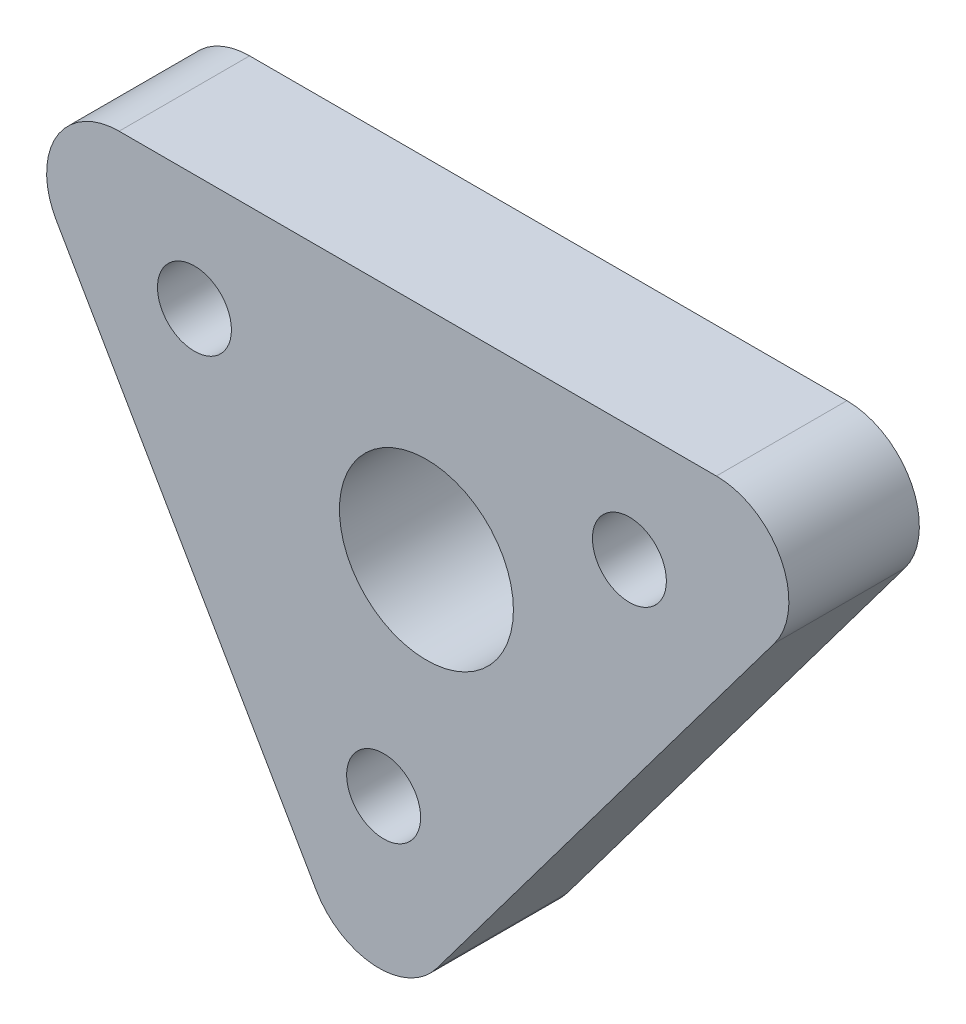
SolidWorks part; units mm, degrees
ref_plane "前视基准面" through (0, 0, 0) normal (0, 0, 1) x (1, 0, 0)
ref_plane "上视基准面" through (0, 0, 0) normal (0, 1, 0) x (1, 0, 0)
ref_plane "右视基准面" through (0, 0, 0) normal (1, 0, 0) x (0, 0, -1)
sketch "草图1" plane through (0, 0, 0) normal (0, 0, 1) x (1, 0, 0)
  line L0 (-40.197, 19.3205) -> (-10.197, 19.3205) construction
  line L1 (-54.0535, 27.3205) -> (5.803, 27.3205)
  line L2 (-27.1481, -3.2809) -> (-40.197, 19.3205) construction
  line L3 (-40.197, 19.3205) -> (-40.197, -20.6795) construction
  line L4 (-40.197, -20.6795) -> (-10.197, 19.3205) construction
  line L5 (5.803, 27.3205) -> (-28.018, -17.7741)
  line L6 (-28.018, -17.7741) -> (-54.0535, 27.3205)
  circle A0 centre (-40.197, 19.3205) radius 2.55
  circle A1 centre (-27.1481, -3.2809) radius 2.55
  circle A2 centre (-10.197, 19.3205) radius 2.55
  circle A3 centre (-24.197, 12.3205) radius 6
  dimension "D4" = 5.1
  dimension "D9" = 15
  dimension "D10" = 12
  dimension "D1" = 60
  dimension "D2" = 30
  dimension "D3" = 40
  dimension "D5" = 8
  dimension "D6" = 8
  dimension "D7" = 8
  dimension "D8" = 15
extrude "凸台-拉伸1" add sketch "草图1" along normal blind 9
fillet "圆角1" radius 5 3 edges at (-28.018, -17.7741, 4.5) (5.803, 27.3205, 4.5) (-54.0535, 27.3205, 4.5)
